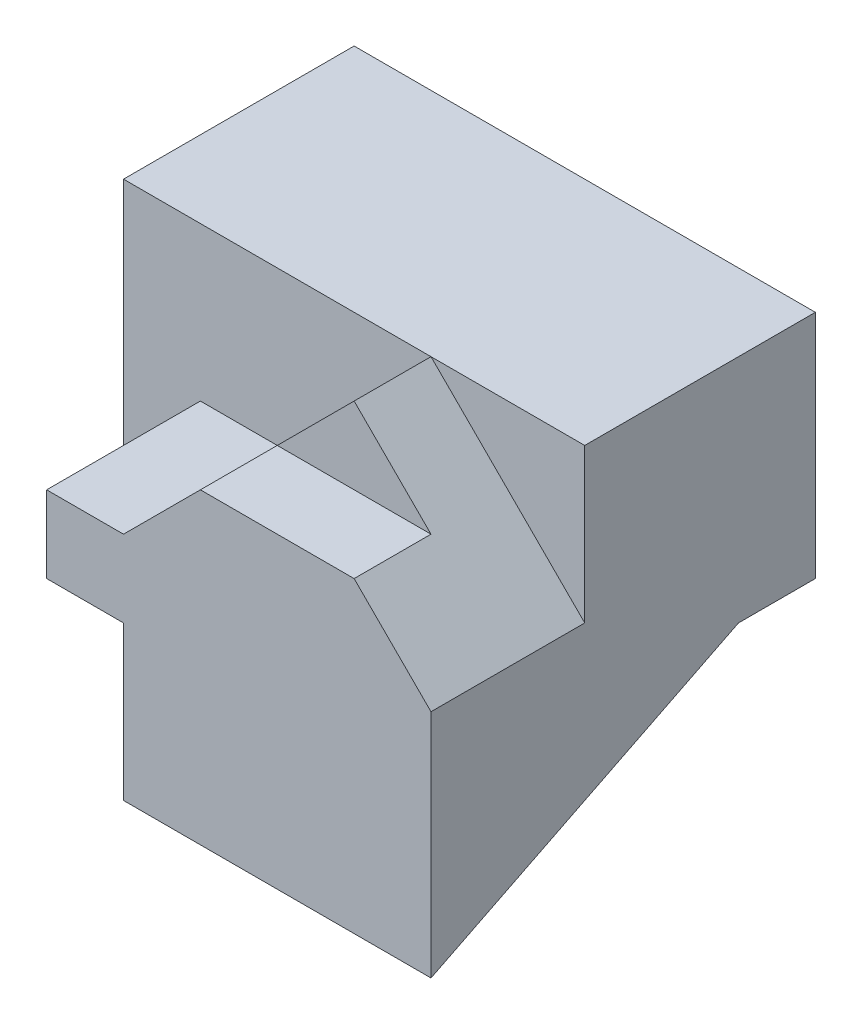
SolidWorks part; units mm, degrees
ref_plane "Front Plane" through (0, 0, 0) normal (0, 0, 1) x (1, 0, 0)
ref_plane "Top Plane" through (0, 0, 0) normal (0, 1, 0) x (1, 0, 0)
ref_plane "Right Plane" through (0, 0, 0) normal (1, 0, 0) x (0, 0, -1)
sketch "Sketch1" plane through (0, 0, 0) normal (0, 0, 1) x (1, 0, 0)
  line L1 (0, 0) -> (6, 0)
  line L2 (0, 0) -> (0, 5)
  line L3 (0, 5) -> (6, 5)
  line L4 (6, 0) -> (6, 5)
  dimension "D1" = 5
  dimension "D2" = 6
extrude "Boss-Extrude1" add sketch "Sketch1" along normal blind 5
sketch "Sketch2" plane through (6, 0, 0) normal (1, 0, 0) x (0, 0, -1)
  line L0 (0, 2) -> (-1, 2)
  line L1 (0, 0) -> (0, 5) construction
  line L2 (-1, 2) -> (-5, 0)
  line L3 (-5, 0) -> (0, 0) construction
  line L4 (-5, 0) -> (0, 0)
  line L5 (0, 0) -> (0, 2)
  dimension "D1" = 2
  dimension "D2" = 1
  dimension "D3" = 5
extrude "Cut-Extrude1" cut sketch "Sketch2" against normal blind 2
sketch "Sketch4" plane through (0, 0, 0) normal (-1, 0, 0) x (0, 0, 1)
  line L0 (1, 0) -> (5, 2)
  line L1 (5, 0) -> (0, 0) construction
  line L2 (5, 5) -> (5, 0) construction
  line L3 (5, 2) -> (5, 0)
  line L4 (5, 0) -> (1, 0)
  dimension "D1" = 1
  dimension "D2" = 2
extrude "Cut-Extrude2" cut sketch "Sketch4" against normal blind 2
sketch "Sketch5" plane through (0, 5, 0) normal (0, 1, 0) x (1, 0, 0)
  line L1 (0, -5) -> (1, -5)
  line L2 (0, -5) -> (0, -3)
  line L3 (0, -3) -> (1, -3)
  line L4 (1, -5) -> (1, -3)
  dimension "D1" = 1
  dimension "D2" = 2
extrude "Cut-Extrude3" cut sketch "Sketch5" against normal blind 5
sketch "Sketch6" plane through (0, 0, 5) normal (0, 0, 1) x (1, 0, 0)
  line L0 (4, 5) -> (6, 3)
  line L1 (6, 5) -> (1, 5) construction
  line L2 (6, 0) -> (6, 5) construction
  line L3 (6, 3) -> (6, 5)
  line L4 (6, 5) -> (4, 5)
  dimension "D1" = 2
  dimension "D2" = 2
extrude "Cut-Extrude4" cut sketch "Sketch6" against normal blind 2
sketch "Sketch7" plane through (0, 0, 5) normal (0, 0, 1) x (1, 0, 0)
  line L0 (4, 5) -> (2, 3)
  line L1 (2, 3) -> (1, 3)
  line L2 (1, 2) -> (1, 5) construction
  line L3 (1, 3) -> (1, 5)
  line L4 (1, 5) -> (4, 5)
  dimension "D1" = 2
  dimension "D2" = 1
extrude "Cut-Extrude5" cut sketch "Sketch7" against normal blind 2
sketch "Sketch8" plane through (0, 0, 5) normal (0, 0, 1) x (1, 0, 0)
  line L0 (3, 4) -> (5, 4)
  line L1 (2, 3) -> (4, 5) construction
  line L2 (4, 5) -> (6, 3) construction
  line L3 (5, 4) -> (4, 5)
  line L4 (4, 5) -> (3, 4)
  dimension "D1" = 1
extrude "Cut-Extrude6" cut sketch "Sketch8" against normal blind 1
